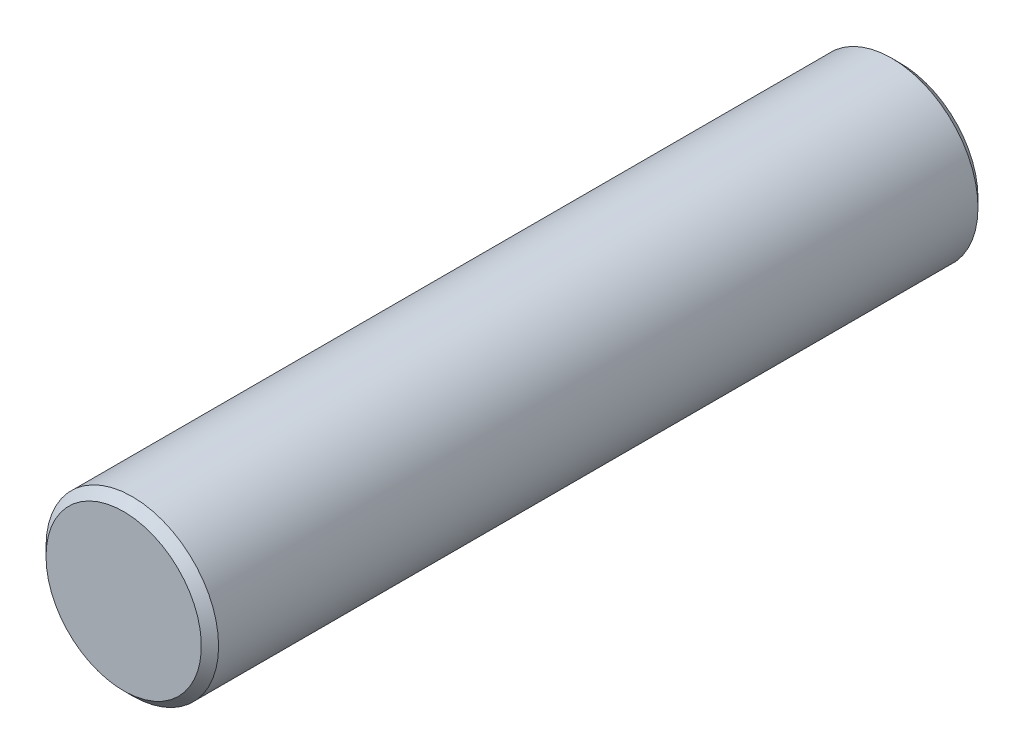
SolidWorks part; units mm, degrees
material "AISI 1020"
ref_plane "Front Plane" through (0, 0, 0) normal (0, 0, 1) x (1, 0, 0)
ref_plane "Top Plane" through (0, 0, 0) normal (0, 1, 0) x (1, 0, 0)
ref_plane "Right Plane" through (0, 0, 0) normal (1, 0, 0) x (0, 0, -1)
sketch "Sketch1" plane through (0, 0, 0) normal (1, 0, 0) x (0, 0, -1)
  line L0 (0, -258.8839) -> (0, 12685.3103) construction
  line L1 (-258.8839, 0) -> (12685.3103, 0) construction
  line L2 (-22.5, 0) -> (22.5, 0)
  line L3 (-22.5, 0) -> (-22.5, 5)
  line L4 (-22.5, 5) -> (22.5, 5)
  line L9 (22.5, 5) -> (22.5, 0)
  point P7 (0, 0)
  point P8 (22.2578, 5)
  dimension "D1" = 45
  dimension "D3" = 10
revolve "Revolve1" add sketch "Sketch1" angle 360 about L1
chamfer "Chamfer1" distance 0.5 angle 45 2 edges at (5, 0, -22.5) (5, 0, 22.5)
